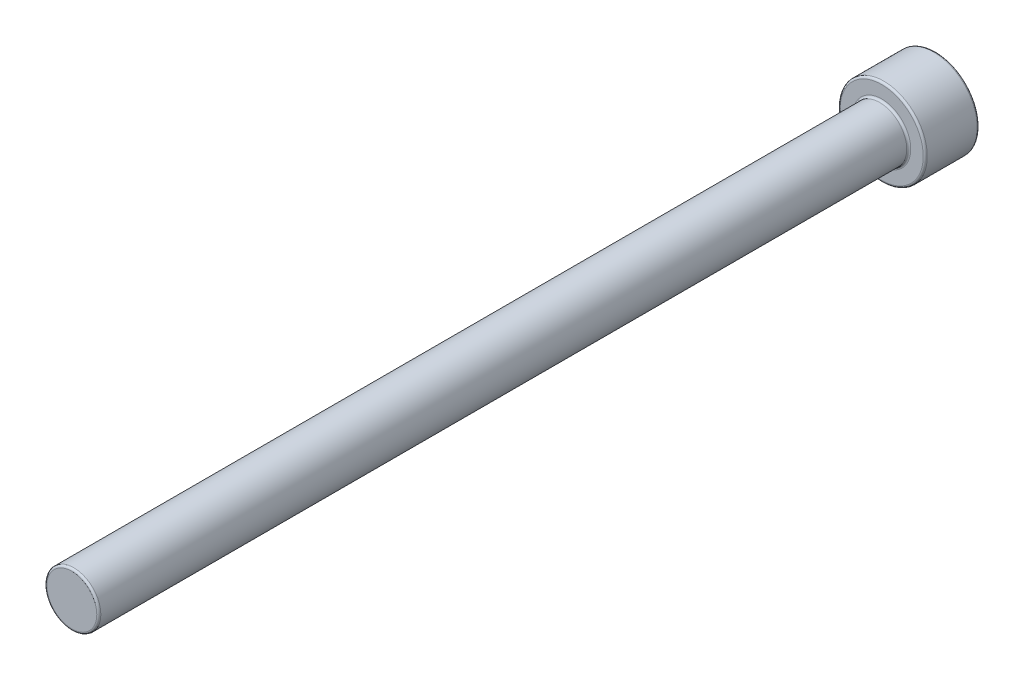
SolidWorks part; units mm, degrees
ref_plane "Спереди" through (0, 0, 0) normal (0, 0, 1) x (1, 0, 0)
ref_plane "Сверху" through (0, 0, 0) normal (0, 1, 0) x (1, 0, 0)
ref_plane "Справа" through (0, 0, 0) normal (1, 0, 0) x (0, 0, -1)
sketch "Эскиз1" plane through (0, 0, 0) normal (0, 0, 1) x (1, 0, 0)
  circle A0 centre (0, 0) radius 4
  dimension "D1" = 8
extrude "Бобышка-Вытянуть1" add sketch "Эскиз1" along normal blind 120
sketch "Эскиз3" plane through (0, 0, 0) normal (0, 0, -1) x (-1, 0, 0)
  circle A0 centre (0, 0) radius 6.45
  dimension "D1" = 12.9
extrude "Бобышка-Вытянуть2" add sketch "Эскиз3" along normal blind 8
sketch "Эскиз4" plane through (0, 0, -8) normal (0, 0, -1) x (-1, 0, 0)
  line L1 (-3.4641, 0) -> (-1.7321, -3)
  line L2 (-1.7321, -3) -> (1.7321, -3)
  line L3 (1.7321, -3) -> (3.4641, 0)
  line L4 (3.4641, 0) -> (1.7321, 3)
  line L5 (1.7321, 3) -> (-1.7321, 3)
  line L6 (-1.7321, 3) -> (-3.4641, 0)
  circle A0 centre (0, 0) radius 3 construction
extrude "Вырез-Вытянуть1" cut sketch "Эскиз4" against normal blind 5
fillet "Скругление1" radius 0.3 16 edges at (-6.45, 0, 0) (4, 0, 0) (-6.45, 0, -8) (2.5981, -1.5, -8) (0, -3, -8) (-2.5981, -1.5, -8) (-2.5981, 1.5, -8) (0, 3, -8) (2.5981, 1.5, -8) (0, 3, -3) (-2.5981, 1.5, -3) (-2.5981, -1.5, -3) (0, -3, -3) (2.5981, -1.5, -3) (2.5981, 1.5, -3) (4, 0, 120)
